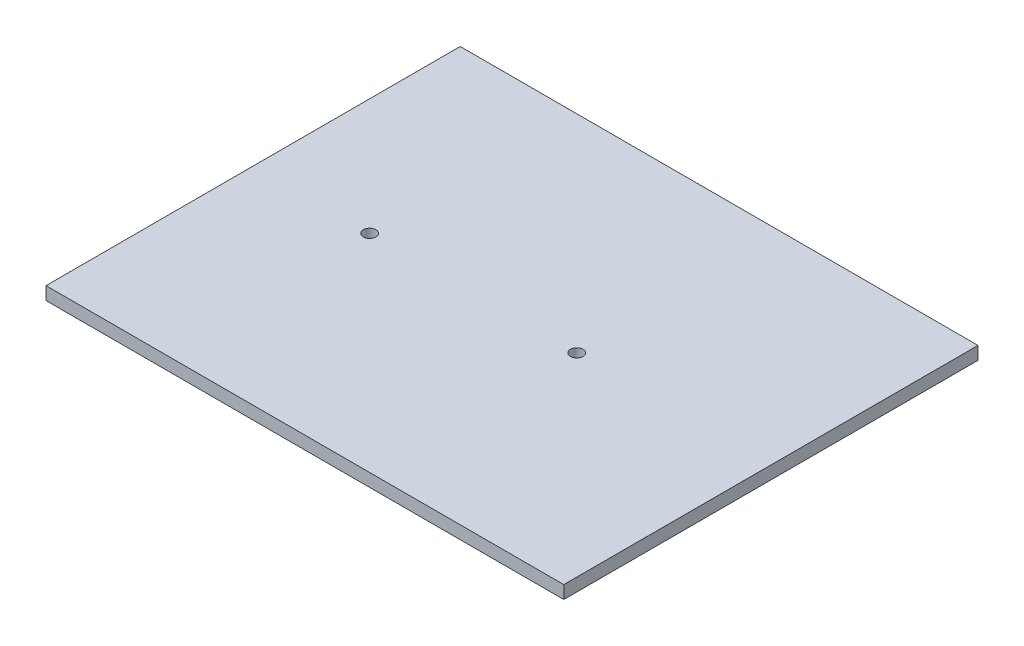
SolidWorks part; units mm, degrees
ref_plane "Front Plane" through (0, 0, 0) normal (0, 0, 1) x (1, 0, 0)
ref_plane "Top Plane" through (0, 0, 0) normal (0, 1, 0) x (1, 0, 0)
ref_plane "Right Plane" through (0, 0, 0) normal (1, 0, 0) x (0, 0, -1)
sketch "Sketch1" plane through (0, 0, 0) normal (0, 1, 0) x (1, 0, 0)
  line L0 (-127, 0) -> (127, 0) construction
  line L1 (-127, 101.6) -> (127, 101.6)
  line L2 (-127, 101.6) -> (-127, -101.6)
  line L3 (-127, -101.6) -> (127, -101.6)
  line L4 (127, 101.6) -> (127, -101.6)
  line L5 (-127, 101.6) -> (127, -101.6) construction
  line L6 (-127, -101.6) -> (127, 101.6) construction
  line L7 (-69.85, 0) -> (31.75, 0)
  circle A0 centre (-69.85, 0) radius 3.0861
  circle A1 centre (31.75, 0) radius 3.0861
  point P0 (-19.05, 0)
  point P11 (-19.05, 0)
  dimension "D4" = 6.1722
  dimension "D5" = 6.1722
  dimension "D1" = 254
  dimension "D2" = 203.2
  dimension "D3" = 101.6
extrude "Boss-Extrude1" add sketch "Sketch1" along normal blind 6.35
